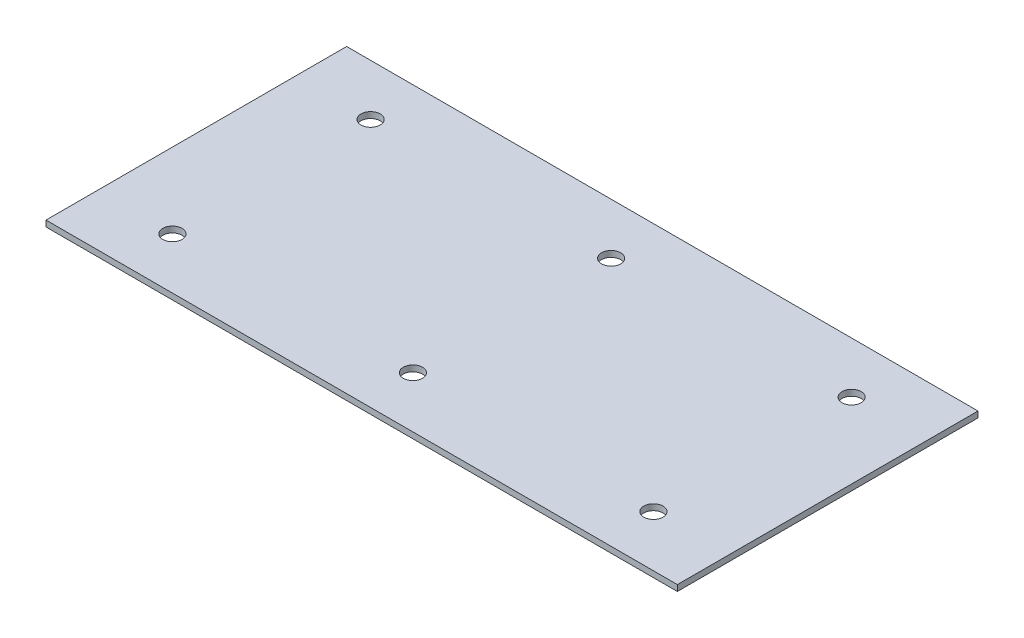
SolidWorks part; units mm, degrees
ref_plane "Спереди" through (0, 0, 0) normal (0, 0, 1) x (1, 0, 0)
ref_plane "Сверху" through (0, 0, 0) normal (0, 1, 0) x (1, 0, 0)
ref_plane "Справа" through (0, 0, 0) normal (1, 0, 0) x (0, 0, -1)
sketch "Эскиз1" plane through (0, 0, 0) normal (0, 1, 0) x (1, 0, 0)
  line L0 (185, 17.0342) -> (25, 17.0342) construction
  line L5 (0, 0) -> (210, 0)
  line L6 (0, 0) -> (0, 100)
  line L7 (0, 100) -> (210, 100)
  line L8 (210, 0) -> (210, 100)
  line L9 (210, 50) -> (0, 50) construction
  circle A0 centre (25, 17.0342) radius 3.2
  circle A1 centre (185, 17.0342) radius 3.2
  circle A2 centre (105, 17.0342) radius 3.2
  circle A3 centre (25, 82.9658) radius 3.2
  circle A4 centre (105, 82.9658) radius 3.2
  circle A5 centre (185, 82.9658) radius 3.2
  dimension "D1" = 210
  dimension "D2" = 100
extrude "Бобышка-Вытянуть1" add sketch "Эскиз1" along normal blind 2
